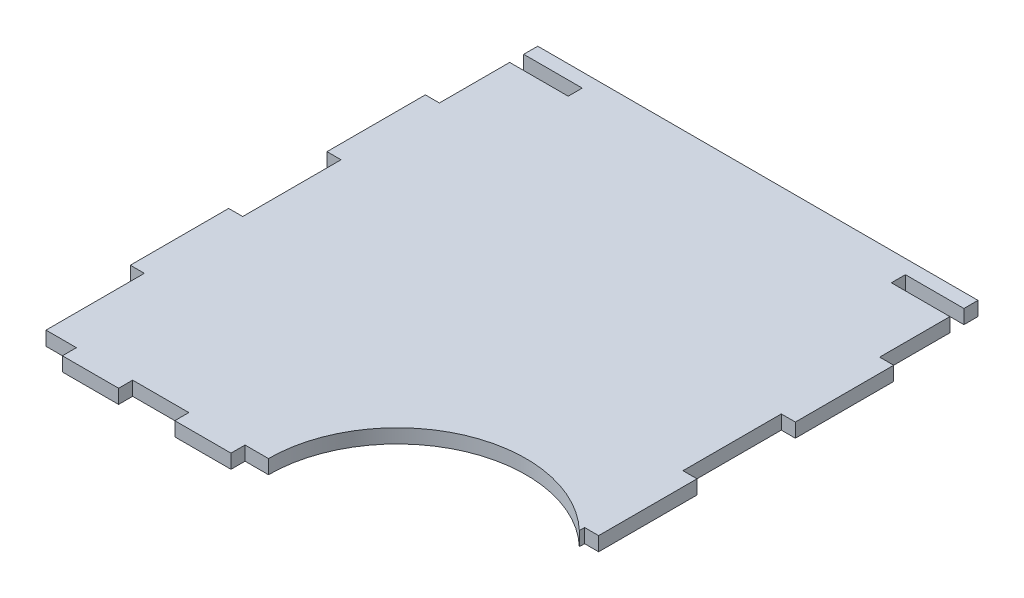
SolidWorks part; units mm, degrees
ref_plane "Front Plane" through (0, 0, 0) normal (0, 0, 1) x (1, 0, 0)
ref_plane "Top Plane" through (0, 0, 0) normal (0, 1, 0) x (1, 0, 0)
ref_plane "Right Plane" through (0, 0, 0) normal (1, 0, 0) x (0, 0, -1)
sketch "Sketch1" plane through (0, 0, 0) normal (0, 1, 0) x (1, 0, 0)
  line L6 (94.2857, 91.0714) -> (94.2857, -161.7074) construction
  line L7 (-115.7143, -118.9286) -> (170.0512, -118.9286) construction
  line L9 (-43.7143, -124.9286) -> (-43.7143, -118.9286)
  line L10 (-43.7143, -118.9286) -> (-67.7143, -118.9286)
  line L11 (-19.7143, -118.9286) -> (-19.7143, -124.9286)
  line L12 (-19.7143, -124.9286) -> (-43.7143, -124.9286)
  line L13 (-67.7143, -118.9286) -> (-67.7143, -124.9286)
  line L14 (-67.7143, -124.9286) -> (-91.7143, -124.9286)
  line L15 (-91.7143, -124.9286) -> (-91.7143, -118.9286)
  line L16 (-91.7143, -118.9286) -> (-104.7143, -118.9286)
  line L19 (-104.7143, 91.0714) -> (83.2857, 91.0714)
  line L21 (-19.7143, -118.9286) -> (-9.7143, -118.9286)
  line L22 (-104.7143, -118.9286) -> (-104.7143, -76.9286)
  line L23 (-104.7143, -76.9286) -> (-110.7143, -76.9286)
  line L24 (-110.7143, -76.9286) -> (-110.7143, -34.9286)
  line L25 (-110.7143, -34.9286) -> (-104.7143, -34.9286)
  line L26 (-104.7143, -34.9286) -> (-104.7143, 7.0714)
  line L27 (-110.7143, 7.0714) -> (-104.7143, 7.0714)
  line L28 (-110.7143, 7.0714) -> (-110.7143, 49.0714)
  line L29 (-110.7143, 49.0714) -> (-104.7143, 49.0714)
  line L31 (-10.7143, 91.0714) -> (-10.7143, -146.3441) construction
  line L33 (83.2857, -76.9286) -> (89.2857, -76.9286)
  line L34 (89.2857, -76.9286) -> (89.2857, -34.9286)
  line L35 (89.2857, -34.9286) -> (83.2857, -34.9286)
  line L36 (83.2857, -34.9286) -> (83.2857, 7.0714)
  line L37 (89.2857, 7.0714) -> (83.2857, 7.0714)
  line L38 (89.2857, 7.0714) -> (89.2857, 49.0714)
  line L39 (89.2857, 49.0714) -> (83.2857, 49.0714)
  line L41 (83.2857, -79.1668) -> (83.2857, -76.9286)
  line L42 (-104.7143, 91.0714) -> (-104.7143, 85.0714)
  line L47 (-104.7143, 85.0714) -> (-79.7143, 85.0714)
  line L48 (-79.7143, 85.0714) -> (-79.7143, 79.0714)
  line L49 (-79.7143, 79.0714) -> (-104.7143, 79.0714)
  line L50 (-104.7143, 79.0714) -> (-104.7143, 49.0714)
  line L51 (83.2857, 79.0714) -> (83.2857, 49.0714)
  line L52 (58.2857, 79.0714) -> (83.2857, 79.0714)
  line L53 (58.2857, 85.0714) -> (58.2857, 79.0714)
  line L54 (83.2857, 85.0714) -> (58.2857, 85.0714)
  line L55 (83.2857, 91.0714) -> (83.2857, 85.0714)
  arc A2 (83.2857, -79.1668) -> (-9.7143, -118.9286) centre (45.2857, -118.9286) ccw
  point P27 (-98.2143, -118.9286)
  dimension "D3" = 55
  dimension "D4" = 188
  dimension "D2" = 49
  dimension "D5" = 114
  dimension "D6" = 24
  dimension "D7" = 6
  dimension "D8" = 6
  dimension "D9" = 24
  dimension "D10" = 24
  dimension "D11" = 13
  dimension "D12" = 42
  dimension "D13" = 84
  dimension "D14" = 126
  dimension "D15" = 168
  dimension "D16" = 210
  dimension "D17" = 25
  dimension "D18" = 6
extrude "Boss-Extrude1" add sketch "Sketch1" along normal blind 6
